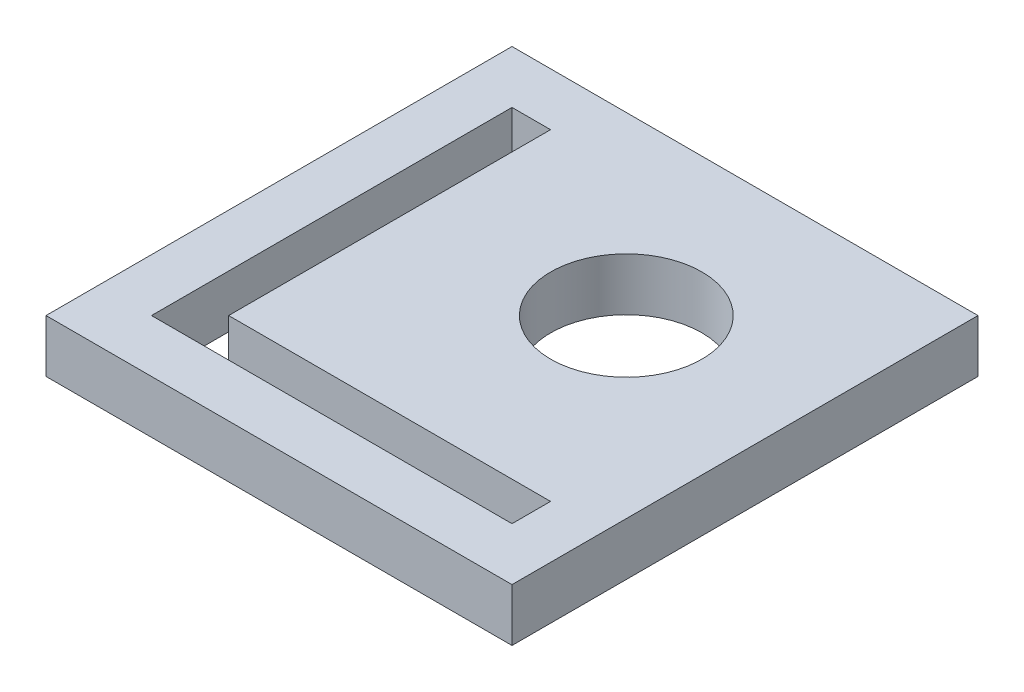
SolidWorks part; units mm, degrees
ref_plane "Front Plane" through (0, 0, 0) normal (0, 0, 1) x (1, 0, 0)
ref_plane "Top Plane" through (0, 0, 0) normal (0, 1, 0) x (1, 0, 0)
ref_plane "Right Plane" through (0, 0, 0) normal (1, 0, 0) x (0, 0, -1)
sketch "Sketch1" plane through (0, 0, 0) normal (0, 1, 0) x (1, 0, 0)
  line L0 (3, 23.5) -> (3, 3)
  line L5 (0, 0) -> (26.5, 0)
  line L6 (0, 0) -> (0, 26.5)
  line L7 (0, 26.5) -> (26.5, 26.5)
  line L8 (26.5, 0) -> (26.5, 26.5)
  line L9 (3, 3) -> (23.5, 3)
  line L10 (23.5, 3) -> (23.5, 5.1934)
  line L11 (23.5, 5.1934) -> (5.1934, 5.1934)
  line L12 (5.1934, 5.1934) -> (5.1934, 23.5)
  line L13 (5.1934, 23.5) -> (3, 23.5)
  point P7 (19.2353, 12.5)
  point P12 (16.8051, 16.8051)
  dimension "D1" = 3
  dimension "D2" = 3
  dimension "D3" = 3
  dimension "D4" = 3
  dimension "D5" = 20.5
  dimension "D6" = 2.1934
extrude "Boss-Extrude1" add sketch "Sketch1" along normal blind 3
sketch "Sketch2" plane through (0, 3, 0) normal (0, 1, 0) x (1, 0, 0)
  line L0 (26.5, 0) -> (26.5, 26.5) construction
  line L1 (26.5, 26.5) -> (0, 26.5) construction
  circle A0 centre (16.5, 16.5) radius 4.3
  dimension "D1" = 8.6
  dimension "D2" = 10
  dimension "D3" = 10
extrude "Cut-Extrude1" cut sketch "Sketch2" against normal through all
equation "\"8mm hole\" = 8.6mm"
equation "\"22mm hole\"= 23mm"
equation "\"15mm hole\"= 15.8mm"
equation "\"bed height offset\"= 3mm"
equation "\"motor width\"= 42.5mm"
equation "\"D1@Sketch2\"= \"8mm hole\""
